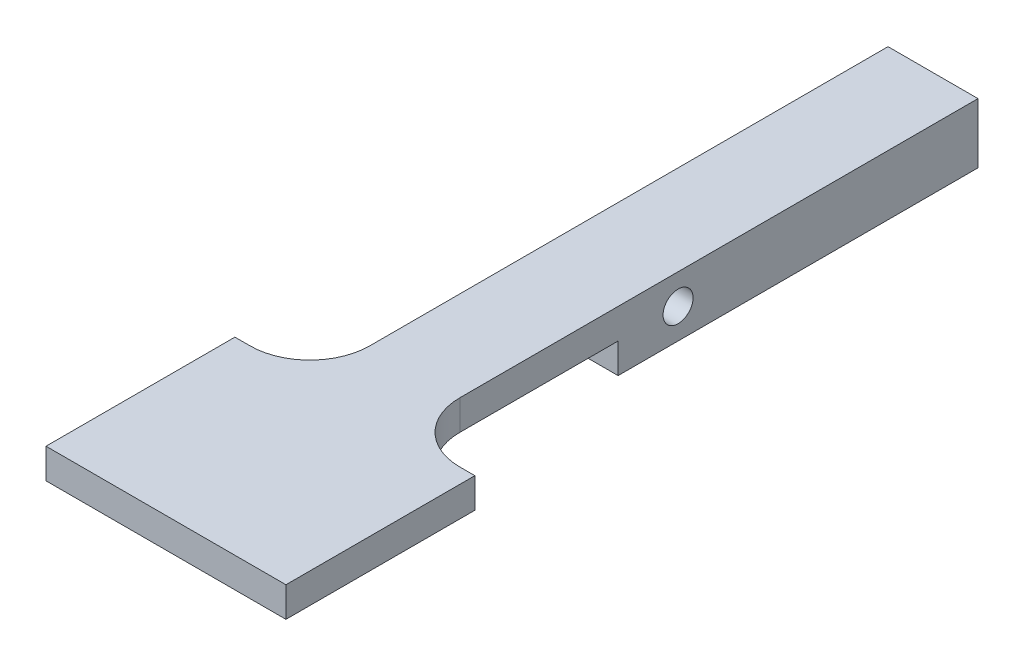
SolidWorks part; units mm, degrees
material "6061 Alloy"
ref_plane "Front Plane" through (0, 0, 0) normal (0, 0, 1) x (1, 0, 0)
ref_plane "Top Plane" through (0, 0, 0) normal (0, 1, 0) x (1, 0, 0)
ref_plane "Right Plane" through (0, 0, 0) normal (1, 0, 0) x (0, 0, -1)
sketch "Sketch1" plane through (0, 0, 0) normal (1, 0, 0) x (0, 0, -1)
  line L0 (0, 1.5875) -> (0, -1.5875)
  line L5 (-76.2, 1.5875) -> (0, 1.5875)
  line L6 (-38.1, -1.5875) -> (-76.2, -1.5875)
  line L8 (-38.1, -1.5875) -> (-38.1, -4.7625)
  line L9 (-38.1, -4.7625) -> (-25.4, -4.7625)
  line L11 (-76.2, 1.5875) -> (-76.2, -1.5875)
  line L12 (-25.4, -4.7625) -> (0, -4.7625)
  line L13 (0, -4.7625) -> (0, -1.5875)
  circle A0 centre (-31.75, -1.5875) radius 1.5875
  point P14 (-31.75, -4.7625)
  dimension "D6" = 3.175
  dimension "D1" = 3.175
  dimension "D4" = 76.2
  dimension "D5" = 3.175
  dimension "D7" = 12.7
  dimension "D8" = 38.1
extrude "Boss-Extrude1" add sketch "Sketch1" along normal blind 9.525
ref_plane "Center Plane" through (4.7625, 0, 0) normal (1, 0, 0) x (0, 0, -1)
sketch "Sketch3" plane through (4.7625, 0, 0) normal (1, 0, 0) x (0, 0, -1)
  line L2 (-76.2, -1.5875) -> (-61.2, -1.5875)
  line L4 (-61.2, -1.5875) -> (-61.2, 1.5875)
  line L5 (-76.2, 1.5875) -> (0, 1.5875) construction
  line L6 (-61.2, 1.5875) -> (-76.2, 1.5875)
  line L7 (-76.2, 1.5875) -> (-76.2, -1.5875)
  line L9 (-76.2, 1.5875) -> (-81.2, 1.5875)
  line L10 (-76.2, 1.5875) -> (-76.2, -1.5875)
  line L11 (-76.2, -1.5875) -> (-81.2, -1.5875)
  line L12 (-81.2, 1.5875) -> (-81.2, -1.5875)
  line L13 (-76.2, 1.5875) -> (-76.2, -1.5875) construction
  line L14 (-38.1, -1.5875) -> (-76.2, -1.5875) construction
  dimension "D1" = 15
  dimension "D2" = 20
extrude "Boss-Extrude2" add sketch "Sketch3" along normal mid plane 25.4 contours L6 L7 L2 L4 | L9 L12 L11 L7
fillet "Fillet1" radius 6.35 2 edges at (0, 0, 61.2) (9.525, 0, 61.2)
